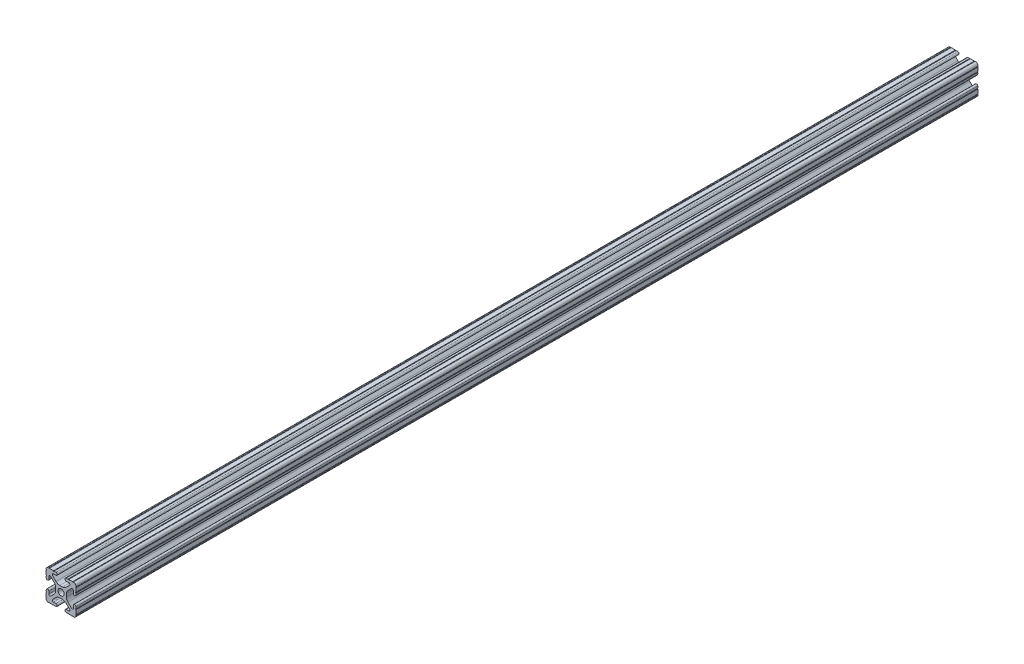
SolidWorks part; units mm, degrees
ref_plane "Front Plane" through (0, 0, 0) normal (0, 0, 1) x (1, 0, 0)
ref_plane "Top Plane" through (0, 0, 0) normal (0, 1, 0) x (1, 0, 0)
ref_plane "Right Plane" through (0, 0, 0) normal (1, 0, 0) x (0, 0, -1)
sketch "Sketch1" plane through (0, 0, 0) normal (0, 0, 1) x (1, 0, 0)
  line L0 (0, 12.7) -> (-12.7814, 12.7) construction
  line L1 (-4.5085, 0) -> (-4.5085, 2.9459)
  line L2 (-6.0437, 12.5461) -> (-10.0976, 12.6876) construction
  line L3 (-11.5616, 12.4229) -> (-4.3159, 12.1699) construction
  line L4 (-6.4364, 10.3486) -> (-6.3592, 12.5571) construction
  line L6 (-2.9459, 4.5085) -> (0, 4.5085)
  line L7 (0, 0) -> (0, 12.7) construction
  line L8 (0, 0) -> (-12.7814, 0) construction
  line L9 (0.7813, 0.7813) -> (-0.7813, -0.7813) construction
  line L10 (-2.9459, 4.5085) -> (-7.1484, 8.711)
  line L11 (-4.5085, 2.9459) -> (-8.711, 7.1484)
  line L13 (0, 0) -> (-12.7814, 12.7814) construction
  line L14 (-10.4131, 12.6987) -> (-4.3048, 12.4853)
  line L15 (-4.3048, 12.4853) -> (-4.382, 10.2769) construction
  line L16 (-4.382, 10.2769) -> (-6.4364, 10.3486)
  line L17 (-12.6987, 10.4131) -> (-12.4853, 4.3048)
  line L18 (-10.2769, 4.382) -> (-10.3486, 6.4364)
  circle A0 centre (0, 0) radius 2.6035
  arc A1 (-4.382, 10.2769) -> (-4.3048, 12.4853) centre (-4.3434, 11.3811) ccw
  arc A2 (-7.1484, 8.711) -> (-6.4364, 10.3486) centre (-6.4698, 9.3896) cw
  arc A3 (-8.711, 7.1484) -> (-10.3486, 6.4364) centre (-9.3896, 6.4698) ccw
  arc A4 (-10.2769, 4.382) -> (-12.4853, 4.3048) centre (-11.3811, 4.3434) cw
  arc A5 (-10.4131, 12.6987) -> (-12.6987, 10.4131) centre (-10.4902, 10.4902) ccw
  arc A6 (-10.4131, 12.6987) -> (-9.7821, 12.6766) centre (-10.0976, 12.6876) ccw
  arc A7 (-6.3592, 12.5571) -> (-5.7282, 12.5351) centre (-6.0437, 12.5461) ccw
  arc A8 (-12.5571, 6.3592) -> (-12.5351, 5.7282) centre (-12.5461, 6.0437) cw
  arc A9 (-12.6987, 10.4131) -> (-12.6766, 9.7821) centre (-12.6876, 10.0976) cw
  dimension "D1" = 5.207
  dimension "D5" = 14.859
  dimension "D9" = 2
  dimension "D2" = 25.4
  dimension "D12" = 0.6314
  dimension "D10" = 2.2098
  dimension "D3" = 9.017
  dimension "D4" = 9.017
  dimension "D6" = 25.4
  dimension "D7" = 6.477
  dimension "D8" = 2.2098
  dimension "D11" = 12.7
sketch "Sketch3" plane through (0, 0, 0) normal (0, 0, 1) x (1, 0, 0)
  line L0 (-2.9459, 4.5085) -> (0, 4.5085) construction
  line L1 (-2.9459, 4.5085) -> (-7.1484, 8.711) construction
  line L2 (-4.382, 10.2769) -> (-6.4364, 10.3486) construction
  line L3 (-10.4131, 12.6987) -> (-4.3048, 12.4853) construction
  line L4 (-4.5085, 0) -> (-4.5085, 2.9459) construction
  line L5 (-4.5085, 2.9459) -> (-8.711, 7.1484) construction
  line L6 (-10.2769, 4.382) -> (-10.3486, 6.4364) construction
  line L7 (-12.6987, 10.4131) -> (-12.4853, 4.3048) construction
  line L8 (-1.1153, 4.5085) -> (1.1153, 4.5085)
  line L9 (-4.2404, 5.803) -> (-7.1484, 8.711)
  line L10 (-4.382, 10.2769) -> (-6.4364, 10.3486)
  line L11 (-9.7821, 12.6766) -> (-6.3592, 12.5571)
  line L12 (-4.5085, -1.1153) -> (-4.5085, 1.1153)
  line L13 (-5.803, 4.2404) -> (-8.711, 7.1484)
  line L14 (-10.2769, 4.382) -> (-10.3486, 6.4364)
  line L15 (-12.6766, 9.7821) -> (-12.5571, 6.3592)
  line L16 (-5.7282, 12.5351) -> (-4.3048, 12.4853)
  line L17 (-12.5351, 5.7282) -> (-12.4853, 4.3048)
  line L18 (0, 0) -> (0, 12.7) construction
  line L19 (0, 0) -> (-12.7814, 0) construction
  line L20 (12.5351, 5.7282) -> (12.4853, 4.3048)
  line L21 (5.7282, 12.5351) -> (4.3048, 12.4853)
  line L22 (12.6766, 9.7821) -> (12.5571, 6.3592)
  line L23 (10.2769, 4.382) -> (10.3486, 6.4364)
  line L24 (5.803, 4.2404) -> (8.711, 7.1484)
  line L25 (4.5085, -1.1153) -> (4.5085, 1.1153)
  line L26 (9.7821, 12.6766) -> (6.3592, 12.5571)
  line L27 (4.382, 10.2769) -> (6.4364, 10.3486)
  line L28 (4.2404, 5.803) -> (7.1484, 8.711)
  line L29 (4.2404, -5.803) -> (7.1484, -8.711)
  line L30 (4.382, -10.2769) -> (6.4364, -10.3486)
  line L31 (9.7821, -12.6766) -> (6.3592, -12.5571)
  line L32 (5.803, -4.2404) -> (8.711, -7.1484)
  line L33 (10.2769, -4.382) -> (10.3486, -6.4364)
  line L34 (12.6766, -9.7821) -> (12.5571, -6.3592)
  line L35 (5.7282, -12.5351) -> (4.3048, -12.4853)
  line L36 (12.5351, -5.7282) -> (12.4853, -4.3048)
  line L37 (-12.5351, -5.7282) -> (-12.4853, -4.3048)
  line L38 (-5.7282, -12.5351) -> (-4.3048, -12.4853)
  line L39 (-12.6766, -9.7821) -> (-12.5571, -6.3592)
  line L40 (-10.2769, -4.382) -> (-10.3486, -6.4364)
  line L41 (-5.803, -4.2404) -> (-8.711, -7.1484)
  line L42 (-9.7821, -12.6766) -> (-6.3592, -12.5571)
  line L43 (-4.382, -10.2769) -> (-6.4364, -10.3486)
  line L44 (-4.2404, -5.803) -> (-7.1484, -8.711)
  line L45 (-1.1153, -4.5085) -> (1.1153, -4.5085)
  arc A0 (-10.4131, 12.6987) -> (-9.7821, 12.6766) centre (-10.0976, 12.6876) ccw construction
  arc A1 (-6.4364, 10.3486) -> (-7.1484, 8.711) centre (-6.4698, 9.3896) ccw construction
  arc A2 (-4.382, 10.2769) -> (-4.3048, 12.4853) centre (-4.3434, 11.3811) ccw construction
  arc A3 (-8.711, 7.1484) -> (-10.3486, 6.4364) centre (-9.3896, 6.4698) ccw construction
  arc A4 (-12.4853, 4.3048) -> (-10.2769, 4.382) centre (-11.3811, 4.3434) ccw construction
  arc A5 (-6.3592, 12.5571) -> (-5.7282, 12.5351) centre (-6.0437, 12.5461) ccw construction
  arc A6 (-10.4131, 12.6987) -> (-12.6987, 10.4131) centre (-10.4902, 10.4902) ccw construction
  arc A7 (-12.6766, 9.7821) -> (-12.6987, 10.4131) centre (-12.6876, 10.0976) ccw construction
  arc A8 (-12.5351, 5.7282) -> (-12.5571, 6.3592) centre (-12.5461, 6.0437) ccw construction
  arc A9 (-10.4131, 12.6987) -> (-9.7821, 12.6766) centre (-10.0976, 12.6876) ccw
  arc A10 (-6.4364, 10.3486) -> (-7.1484, 8.711) centre (-6.4698, 9.3896) ccw
  arc A11 (-4.382, 10.2769) -> (-4.3048, 12.4853) centre (-4.3434, 11.3811) ccw
  arc A12 (-8.711, 7.1484) -> (-10.3486, 6.4364) centre (-9.3896, 6.4698) ccw
  arc A13 (-12.4853, 4.3048) -> (-10.2769, 4.382) centre (-11.3811, 4.3434) ccw
  arc A14 (-6.3592, 12.5571) -> (-5.7282, 12.5351) centre (-6.0437, 12.5461) ccw
  arc A15 (-10.4131, 12.6987) -> (-12.6987, 10.4131) centre (-10.4902, 10.4902) ccw
  arc A16 (-12.6766, 9.7821) -> (-12.6987, 10.4131) centre (-12.6876, 10.0976) ccw
  arc A17 (-12.5351, 5.7282) -> (-12.5571, 6.3592) centre (-12.5461, 6.0437) ccw
  arc A18 (-1.1153, 4.5085) -> (-4.2404, 5.803) centre (-1.1153, 8.9281) cw
  arc A19 (4.5085, 1.1153) -> (5.803, 4.2404) centre (8.9281, 1.1153) cw
  arc A20 (1.1153, 4.5085) -> (4.2404, 5.803) centre (1.1153, 8.9281) ccw
  arc A21 (-4.5085, 1.1153) -> (-5.803, 4.2404) centre (-8.9281, 1.1153) ccw
  arc A22 (12.5351, 5.7282) -> (12.5571, 6.3592) centre (12.5461, 6.0437) cw
  arc A23 (12.6766, 9.7821) -> (12.6987, 10.4131) centre (12.6876, 10.0976) cw
  arc A24 (10.4131, 12.6987) -> (12.6987, 10.4131) centre (10.4902, 10.4902) cw
  arc A25 (6.3592, 12.5571) -> (5.7282, 12.5351) centre (6.0437, 12.5461) cw
  arc A26 (12.4853, 4.3048) -> (10.2769, 4.382) centre (11.3811, 4.3434) cw
  arc A27 (8.711, 7.1484) -> (10.3486, 6.4364) centre (9.3896, 6.4698) cw
  arc A28 (4.382, 10.2769) -> (4.3048, 12.4853) centre (4.3434, 11.3811) cw
  arc A29 (6.4364, 10.3486) -> (7.1484, 8.711) centre (6.4698, 9.3896) cw
  arc A30 (10.4131, 12.6987) -> (9.7821, 12.6766) centre (10.0976, 12.6876) cw
  arc A31 (10.4131, -12.6987) -> (9.7821, -12.6766) centre (10.0976, -12.6876) ccw
  arc A32 (6.4364, -10.3486) -> (7.1484, -8.711) centre (6.4698, -9.3896) ccw
  arc A33 (4.382, -10.2769) -> (4.3048, -12.4853) centre (4.3434, -11.3811) ccw
  arc A34 (8.711, -7.1484) -> (10.3486, -6.4364) centre (9.3896, -6.4698) ccw
  arc A35 (12.4853, -4.3048) -> (10.2769, -4.382) centre (11.3811, -4.3434) ccw
  arc A36 (6.3592, -12.5571) -> (5.7282, -12.5351) centre (6.0437, -12.5461) ccw
  arc A37 (10.4131, -12.6987) -> (12.6987, -10.4131) centre (10.4902, -10.4902) ccw
  arc A38 (12.6766, -9.7821) -> (12.6987, -10.4131) centre (12.6876, -10.0976) ccw
  arc A39 (12.5351, -5.7282) -> (12.5571, -6.3592) centre (12.5461, -6.0437) ccw
  arc A40 (-4.5085, -1.1153) -> (-5.803, -4.2404) centre (-8.9281, -1.1153) cw
  arc A41 (1.1153, -4.5085) -> (4.2404, -5.803) centre (1.1153, -8.9281) cw
  arc A42 (4.5085, -1.1153) -> (5.803, -4.2404) centre (8.9281, -1.1153) ccw
  arc A43 (-1.1153, -4.5085) -> (-4.2404, -5.803) centre (-1.1153, -8.9281) ccw
  arc A44 (-12.5351, -5.7282) -> (-12.5571, -6.3592) centre (-12.5461, -6.0437) cw
  arc A45 (-12.6766, -9.7821) -> (-12.6987, -10.4131) centre (-12.6876, -10.0976) cw
  arc A46 (-10.4131, -12.6987) -> (-12.6987, -10.4131) centre (-10.4902, -10.4902) cw
  arc A47 (-6.3592, -12.5571) -> (-5.7282, -12.5351) centre (-6.0437, -12.5461) cw
  arc A48 (-12.4853, -4.3048) -> (-10.2769, -4.382) centre (-11.3811, -4.3434) cw
  arc A49 (-8.711, -7.1484) -> (-10.3486, -6.4364) centre (-9.3896, -6.4698) cw
  arc A50 (-4.382, -10.2769) -> (-4.3048, -12.4853) centre (-4.3434, -11.3811) cw
  arc A51 (-6.4364, -10.3486) -> (-7.1484, -8.711) centre (-6.4698, -9.3896) cw
  arc A52 (-10.4131, -12.6987) -> (-9.7821, -12.6766) centre (-10.0976, -12.6876) cw
  circle A53 centre (0, 0) radius 2.6035 construction
  circle A54 centre (0, 0) radius 2.6035
  point P135 (4.5085, 0)
  dimension "D2" = 4.4196
extrude "Extrude1" add sketch "Sketch3" along normal mid plane 760
ref_plane "Plane1" through (12.4853, 4.3048, 380) normal (0.0349, 0.9994, 0) x (0.9994, -0.0349, 0)
equation "\"D10@Sketch1\" = \"D8@Sketch1\""
equation "\"D11@Sketch1\" = \"D6@Sketch1\"/2"
equation "\"D12@Sketch1\" = \"D8@Sketch1\"/3.5"
equation "\"D2@Sketch3\" = \"D8@Sketch1\"*2"
